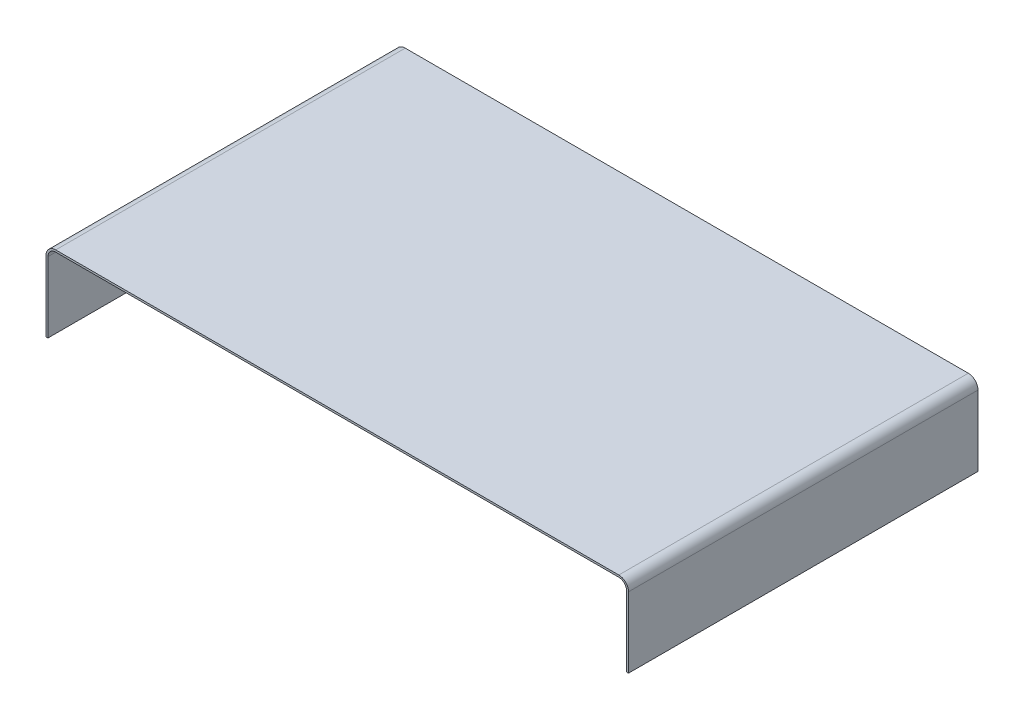
SolidWorks part; units mm, degrees
ref_plane "Plano frontal" through (0, 0, 0) normal (0, 0, 1) x (1, 0, 0)
ref_plane "Plano superior" through (0, 0, 0) normal (0, 1, 0) x (1, 0, 0)
ref_plane "Plano direito" through (0, 0, 0) normal (1, 0, 0) x (0, 0, -1)
sketch "Esboço1" plane through (0, 0, 0) normal (0, 0, 1) x (1, 0, 0)
  line L0 (0, 0) -> (0, 36.3)
  line L1 (300, 0) -> (300, 36.3)
  line L2 (5, 41.3) -> (295, 41.3)
  line L3 (1, 0) -> (1, 36.3)
  line L4 (5, 40.3) -> (295, 40.3)
  line L5 (299, 0) -> (299, 36.3)
  line L6 (0, 0) -> (1, 0)
  line L7 (299, 0) -> (300, 0)
  arc A0 (0, 36.3) -> (5, 41.3) centre (5, 36.3) cw
  arc A1 (300, 36.3) -> (295, 41.3) centre (295, 36.3) ccw
  arc A2 (1, 36.3) -> (5, 40.3) centre (5, 36.3) cw
  arc A3 (299, 36.3) -> (295, 40.3) centre (295, 36.3) ccw
  point P7 (0, 41.3)
  dimension "D3" = 5
  dimension "D4" = 5
  dimension "D1" = 41.3
  dimension "D2" = 300
  dimension "D5" = 1
extrude "Ressalto-extrusão1" add sketch "Esboço1" along normal blind 180
